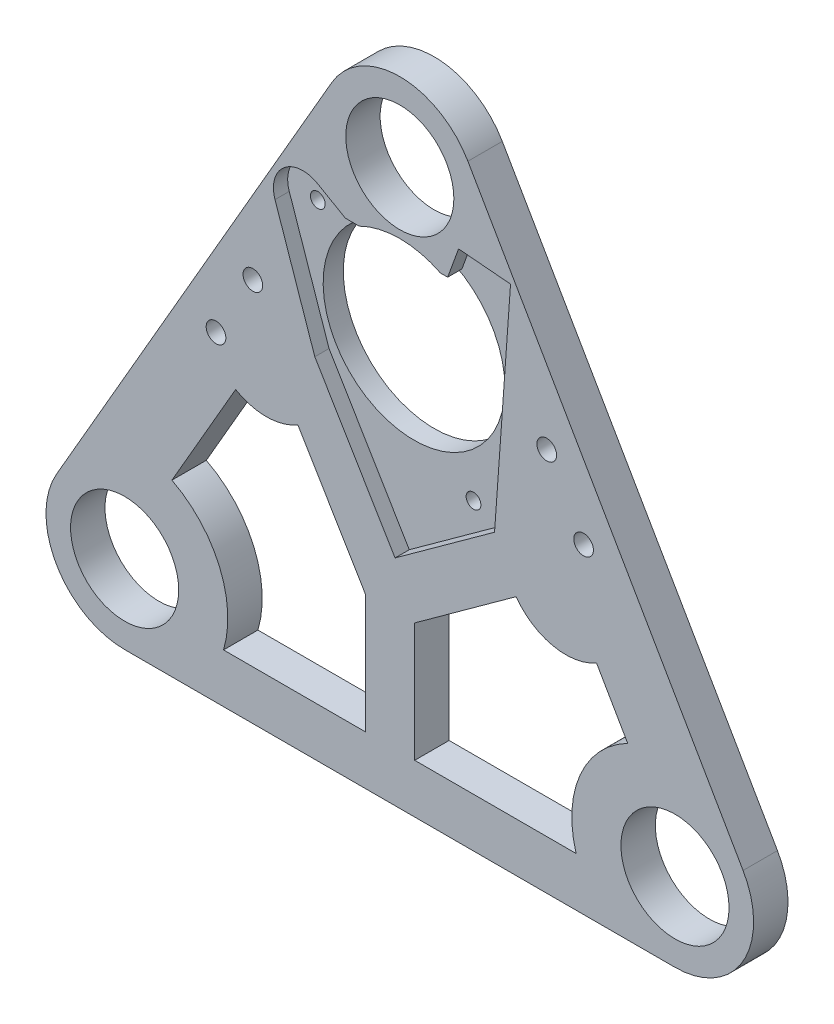
SolidWorks part; units mm, degrees
ref_plane "Front Plane" through (0, 0, 0) normal (0, 0, 1) x (1, 0, 0)
ref_plane "Top Plane" through (0, 0, 0) normal (0, 1, 0) x (1, 0, 0)
ref_plane "Right Plane" through (0, 0, 0) normal (1, 0, 0) x (0, 0, -1)
sketch "Sketch1" plane through (0, 0, 0) normal (0, 0, 1) x (1, 0, 0)
  line L0 (3.85, 0) -> (-3.85, 0) construction
  line L1 (42.1436, 104.9948) -> (-13.8564, 8)
  line L2 (69.8564, 104.9948) -> (125.8564, 8)
  line L3 (0, -16) -> (112, -16)
  circle A0 centre (0, 0) radius 11
  circle A1 centre (112, 0) radius 11
  arc A2 (-13.8564, 8) -> (0, -16) centre (0, 0) ccw
  arc A3 (112, -16) -> (125.8564, 8) centre (112, 0) ccw
  circle A4 centre (56, 96.9948) radius 11
  arc A5 (69.8564, 104.9948) -> (42.1436, 104.9948) centre (56, 96.9948) ccw
  dimension "D1" = 22
  dimension "D2" = 22
  dimension "D3" = 32
  dimension "D4" = 32
  dimension "D5" = 112
  dimension "D6" = 22
  dimension "D7" = 32
  dimension "D8" = 112
  dimension "D9" = 112
extrude "Boss-Extrude1" add sketch "Sketch1" along normal blind 7
sketch "Sketch3" plane through (0, 0, 7) normal (0, 0, 1) x (1, 0, 0)
  line L0 (56, 71.0948) -> (56, 69.0948) construction
  circle A0 centre (56, 96.9948) radius 27.9 construction
  circle A1 centre (56, 65.9448) radius 5.15 construction
  circle A2 centre (56, 65.9448) radius 18.5
  dimension "D1" = 55.8
  dimension "D2" = 10.3
  dimension "D4" = 37
  dimension "D3" = 2
extrude "Cut-Extrude1" cut sketch "Sketch3" against normal through all
sketch "Sketch4" plane through (0, 0, 7) normal (0, 0, 1) x (1, 0, 0)
  line L0 (44.91, 82.4948) -> (65.74, 82.4948)
  line L1 (65.74, 82.4948) -> (67.9631, 88.6028)
  line L2 (67.9631, 88.6028) -> (78.5352, 87.6779)
  line L3 (78.5352, 87.6779) -> (75.2824, 42.3244)
  line L4 (75.2824, 42.3244) -> (55.0308, 27.6659)
  line L5 (55.0308, 27.6659) -> (38.7013, 54.953)
  line L6 (38.7013, 54.953) -> (30.6042, 78.6054)
  line L7 (44.91, 82.4948) -> (39.2808, 85.7448)
  line L8 (56, 65.9448) -> (56, 82.4948) construction
  line L9 (56, 65.9448) -> (63.15, 65.9448) construction
  circle A0 centre (56, 65.9448) radius 7.15 construction
  arc A1 (39.2808, 85.7448) -> (30.6042, 78.6054) centre (36.2808, 80.5487) ccw
  dimension "D1" = 14.3
  dimension "D8" = 12
  dimension "D15" = 16.55
  dimension "D2" = 85
  dimension "D3" = 130
  dimension "D4" = 168
  dimension "D5" = 105
  dimension "D6" = 250
  dimension "D7" = 210
  dimension "D9" = 25
  dimension "D10" = 31.8
  dimension "D11" = 25
  dimension "D12" = 45.47
  dimension "D13" = 6.5
  dimension "D14" = 20.83
  dimension "D16" = 90
  dimension "D17" = 11.09
  dimension "D18" = 6.5
extrude "Cut-Extrude2" cut sketch "Sketch4" against normal blind 2.9
sketch "Sketch5" plane through (0, 0, 7) normal (0, 0, 1) x (1, 0, 0)
  line L0 (22.5915, 41.1297) -> (9.6221, 18.6659)
  line L1 (42.1436, 104.9948) -> (-13.8564, 8) construction
  line L2 (20.1246, -6) -> (49.0315, -6)
  line L3 (35.2604, 41.2289) -> (49.0315, 18.217)
  line L4 (49.0315, 18.217) -> (49.0315, -6)
  line L5 (59.0315, 18.217) -> (59.0315, -6)
  line L6 (38.7013, 54.953) -> (55.0308, 27.6659) construction
  line L7 (38.7013, 54.953) -> (55.0308, 27.6659) construction
  line L8 (0, -16) -> (112, -16) construction
  line L9 (96.0352, 29.6518) -> (102.3779, 18.6659)
  line L10 (125.8564, 8) -> (69.8564, 104.9948) construction
  line L11 (79.6594, 33.1479) -> (59.0315, 18.217)
  line L12 (55.0308, 27.6659) -> (75.2824, 42.3244) construction
  line L13 (59.0315, -6) -> (91.8754, -6)
  line L14 (28.8415, 51.955) -> (22.5915, 41.1297) construction
  line L15 (28.8415, 51.955) -> (35.2604, 41.2289) construction
  line L16 (89.7852, 40.4771) -> (79.6594, 33.1479) construction
  line L17 (89.7852, 40.4771) -> (96.0352, 29.6518) construction
  arc A0 (20.1246, -6) -> (9.6221, 18.6659) centre (0, 0) ccw
  circle A1 centre (0, 0) radius 11 construction
  arc A2 (102.3779, 18.6659) -> (91.8754, -6) centre (112, 0) ccw
  circle A3 centre (112, 0) radius 11 construction
  arc A4 (22.5915, 41.1297) -> (35.2604, 41.2289) centre (28.8415, 51.955) ccw
  arc A5 (79.6594, 33.1479) -> (96.0352, 29.6518) centre (89.7852, 40.4771) ccw
  dimension "D1" = 10
  dimension "D5" = 10
  dimension "D9" = 25
  dimension "D10" = 25
  dimension "D2" = 15
  dimension "D3" = 10
  dimension "D4" = 10
  dimension "D6" = 10
  dimension "D7" = 15
  dimension "D8" = 10
extrude "Cut-Extrude3" cut sketch "Sketch5" against normal through all
sketch "Sketch7" plane through (0, 0, 4.1) normal (0, 0, 1) x (1, 0, 0)
  line L0 (75.2824, 42.3244) -> (68.1009, 42.8395) construction
  line L1 (78.5352, 87.6779) -> (75.2824, 42.3244) construction
  circle A0 centre (68.1009, 42.8395) radius 1.5
  circle A1 centre (36.41, 79.9948) radius 1.5
  dimension "D2" = 3
  dimension "D5" = 3
  dimension "D1" = 7.2
  dimension "D3" = 8.5
  dimension "D4" = 2.5
  dimension "D6" = 90
extrude "Cut-Extrude4" cut sketch "Sketch7" against normal through all
sketch "Sketch10" plane through (0, 0, 7) normal (0, 0, 1) x (1, 0, 0)
  line L0 (26.0963, 62.2002) -> (18.5963, 49.2098) construction
  line L1 (42.1436, 104.9948) -> (-13.8564, 8) construction
  line L2 (28.8415, 51.955) -> (15.8511, 59.455) construction
  line L3 (85.9037, 62.2002) -> (93.4037, 49.2098) construction
  line L4 (125.8564, 8) -> (69.8564, 104.9948) construction
  circle A0 centre (26.0963, 62.2002) radius 2
  circle A1 centre (18.5963, 49.2098) radius 2
  circle A2 centre (85.9037, 62.2002) radius 2
  circle A3 centre (93.4037, 49.2098) radius 2
  point P6 (22.3463, 55.705)
  point P7 (22.3463, 55.705)
  dimension "D1" = 4
  dimension "D2" = 4
  dimension "D4" = 4
  dimension "D5" = 4
  dimension "D3" = 15
  dimension "D6" = 7.5
extrude "Cut-Extrude5" cut sketch "Sketch10" against normal through all
